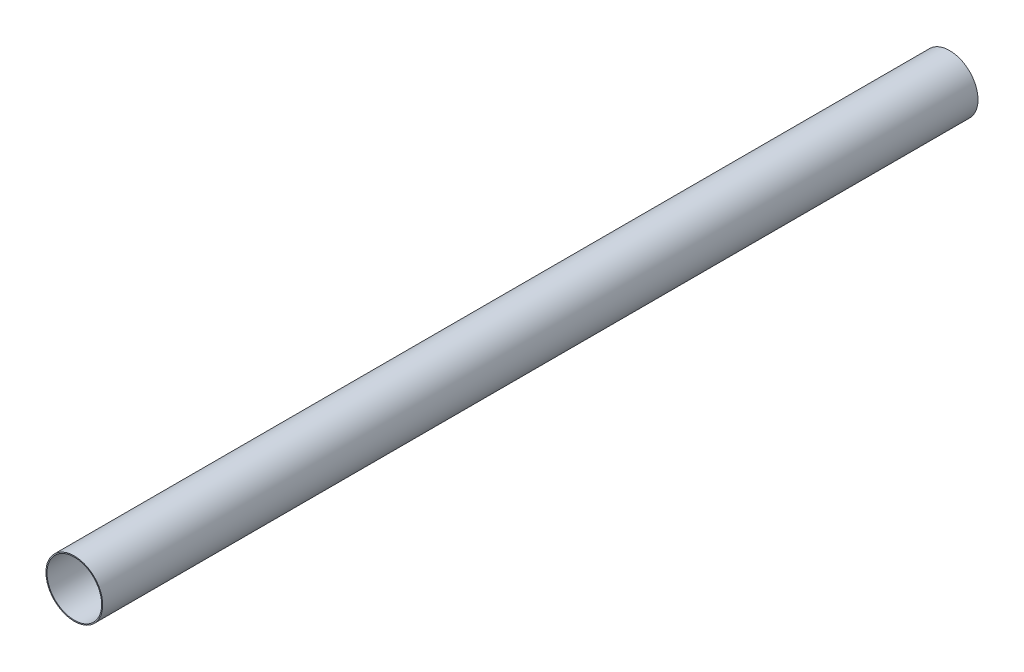
SolidWorks part; units mm, degrees
ref_plane "Front" through (0, 0, 0) normal (0, 0, 1) x (1, 0, 0)
ref_plane "Top" through (0, 0, 0) normal (0, 1, 0) x (1, 0, 0)
ref_plane "Side" through (0, 0, 0) normal (1, 0, 0) x (0, 0, -1)
sketch "PipeSketch" plane through (0, 0, 0) normal (0, 0, 1) x (1, 0, 0)
  circle A0 centre (0, 0) radius 177.8
  circle A1 centre (0, 0) radius 171.45
  dimension "OuterDiameter" = 355.6
  dimension "InnerDiameter" = 342.9
extrude "Extrusion" add sketch "PipeSketch" along normal blind 5486.4
sketch "FilterSketch" plane through (0, 0, 0) normal (0, 0, 1) x (1, 0, 0)
  circle A0 centre (0, 0) radius 177.8 construction
  dimension "NominalDiameter" = 355.6
